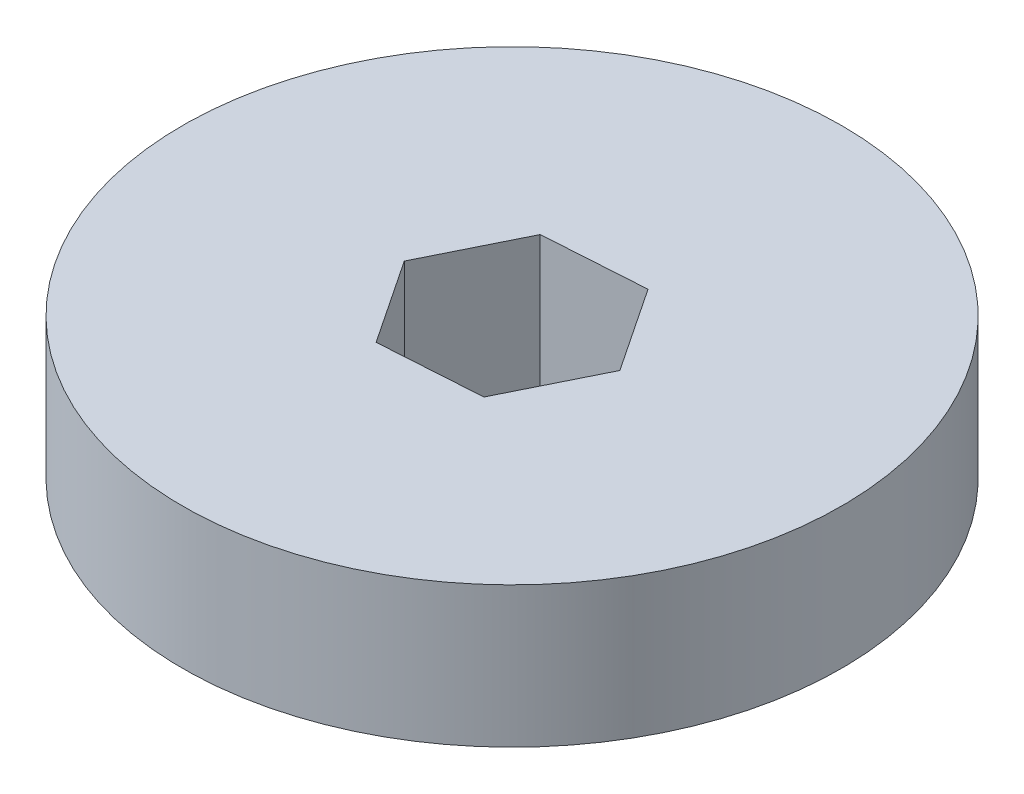
SolidWorks part; units mm, degrees
ref_plane "Front Plane" through (0, 0, 0) normal (0, 0, 1) x (1, 0, 0)
ref_plane "Top Plane" through (0, 0, 0) normal (0, 1, 0) x (1, 0, 0)
ref_plane "Right Plane" through (0, 0, 0) normal (1, 0, 0) x (0, 0, -1)
sketch "Sketch1" plane through (0, 0, 0) normal (0, 1, 0) x (1, 0, 0)
  circle A0 centre (0, 0) radius 30.1625
  dimension "D1" = 60.325
extrude "Boss-Extrude1" add sketch "Sketch1" along normal blind 10.16
sketch "Sketch2" plane through (0, 10.16, 0) normal (0, 1, 0) x (1, 0, 0)
  line L1 (4.0673, -6.1009) -> (7.3171, 0.4719)
  line L2 (7.3171, 0.4719) -> (3.2499, 6.5728)
  line L3 (3.2499, 6.5728) -> (-4.0673, 6.1009)
  line L4 (-4.0673, 6.1009) -> (-7.3171, -0.4719)
  line L5 (-7.3171, -0.4719) -> (-3.2499, -6.5728)
  line L6 (-3.2499, -6.5728) -> (4.0673, -6.1009)
  circle A0 centre (0, 0) radius 6.35 construction
  dimension "D1" = 12.7
extrude "Cut-Extrude1" cut sketch "Sketch2" against normal through all
sketch "Sketch3" plane through (0, 0, 0) normal (0, -1, 0) x (-1, 0, 0)
  circle A0 centre (0, 0) radius 23.8125
  circle A1 centre (0, 0) radius 30.1625 construction
  circle A2 centre (0, 0) radius 30.1625
  dimension "D1" = 6.35
extrude "Cut-Extrude2" cut sketch "Sketch3" against normal through all
